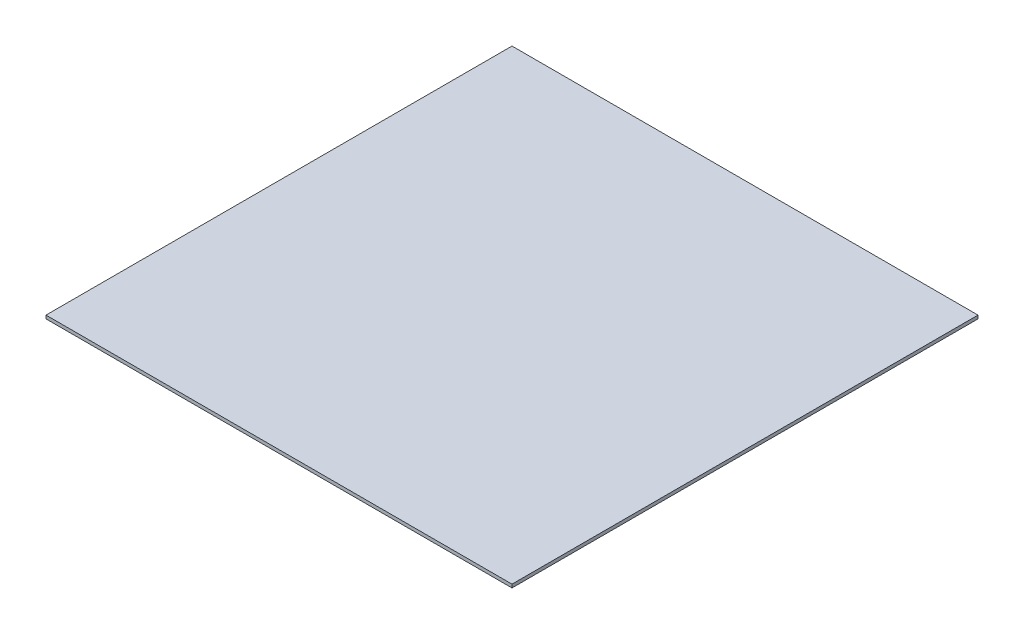
SolidWorks part; units mm, degrees
ref_plane "Front Plane" through (0, 0, 0) normal (0, 0, 1) x (1, 0, 0)
ref_plane "Top Plane" through (0, 0, 0) normal (0, 1, 0) x (1, 0, 0)
ref_plane "Right Plane" through (0, 0, 0) normal (1, 0, 0) x (0, 0, -1)
sketch "Sketch1" plane through (0, 0, 0) normal (0, 1, 0) x (1, 0, 0)
  line L0 (0, 0) -> (107.07, 0)
  line L1 (0, 0) -> (0, 107.07)
  line L2 (0, 107.07) -> (107.07, 107.07)
  line L3 (107.07, 107.07) -> (107.07, 0)
extrude "Boss-Extrude1" add sketch "Sketch1" along normal blind 0.762
scale "Scale1" scale about centroid uniform scaling yes scale factor 0.5
